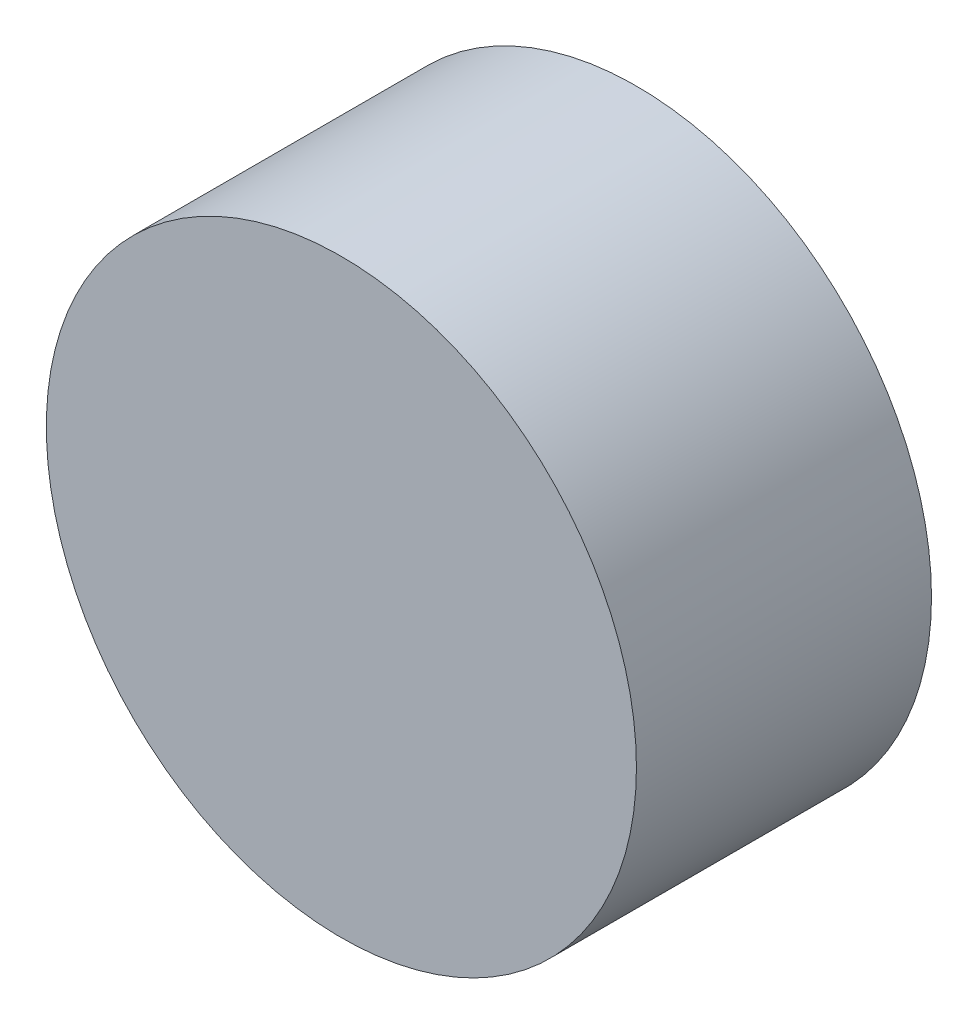
SolidWorks part; units mm, degrees
ref_plane "Alzado" through (0, 0, 0) normal (0, 0, 1) x (1, 0, 0)
ref_plane "Planta" through (0, 0, 0) normal (0, 1, 0) x (1, 0, 0)
ref_plane "Vista lateral" through (0, 0, 0) normal (1, 0, 0) x (0, 0, -1)
sketch "Croquis1" plane through (0, 0, 0) normal (0, 0, 1) x (1, 0, 0)
  circle A0 centre (-2.706, 4.5161) radius 10
  dimension "D1" = 20
extrude "Saliente-Extruir1" add sketch "Croquis1" along normal blind 10
